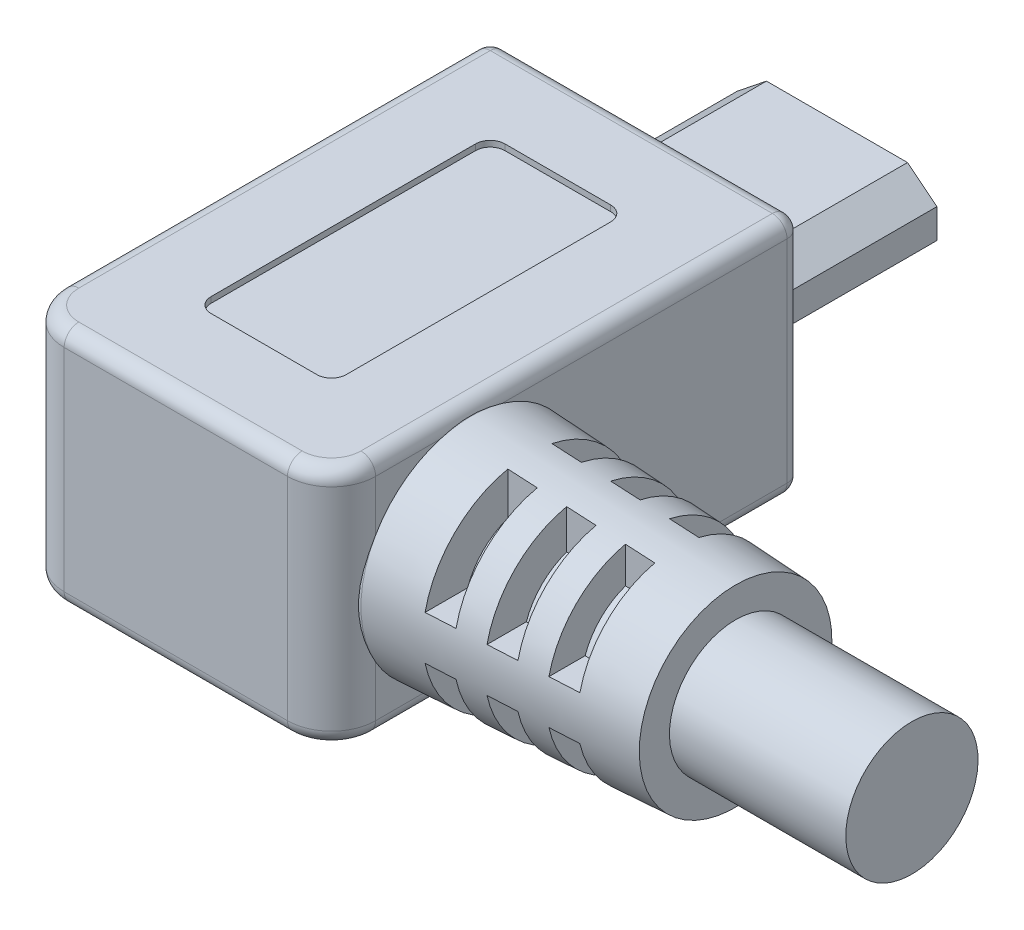
SolidWorks part; units mm, degrees
ref_plane "Front Plane" through (0, 0, 0) normal (0, 0, 1) x (1, 0, 0)
ref_plane "Top Plane" through (0, 0, 0) normal (0, 1, 0) x (1, 0, 0)
ref_plane "Right Plane" through (0, 0, 0) normal (1, 0, 0) x (0, 0, -1)
sketch "Sketch1" plane through (0, 0, 0) normal (0, 0, 1) x (1, 0, 0)
  line L0 (0, 1) -> (1, 1.8)
  line L1 (0, 0) -> (6.8, 0)
  line L2 (0, 0) -> (0, 1.8)
  line L3 (0, 1.8) -> (6.8, 1.8)
  line L4 (6.8, 0) -> (6.8, 1.8)
  line L5 (3.4, 1.8) -> (3.4, 0) construction
  line L6 (6.8, 1) -> (5.8, 1.8)
  line L8 (1.55, 0.2) -> (5.25, 0.2)
  line L9 (1.55, 0.2) -> (1.55, 0.85)
  line L10 (1.55, 0.85) -> (5.25, 0.85)
  line L11 (5.25, 0.2) -> (5.25, 0.85)
  point P15 (3.4, 0.85)
  dimension "D1" = 1.8
  dimension "D2" = 6.8
  dimension "D3" = 1
  dimension "D4" = 1
  dimension "D5" = 0.2
  dimension "D6" = 3.7
  dimension "D7" = 0.65
extrude "Boss-Extrude1" add sketch "Sketch1" along normal blind 6.5 contours L5 L3 L0 L2 L1 L8 L9 L10 | L3 L5 L10 L11 L8 L1 L4 L6
sketch "Sketch2" plane through (0, 0, 6.5) normal (0, 0, 1) x (1, 0, 0)
  line L0 (0, 0.5) -> (-1.9, 0.5) construction
  line L1 (-1.9, 5) -> (8.7, 5)
  line L2 (-1.9, 5) -> (-1.9, -3.2)
  line L3 (-1.9, -3.2) -> (8.7, -3.2)
  line L4 (8.7, 5) -> (8.7, -3.2)
  line L5 (-1.9, 2.8) -> (0.3, 5) construction
  line L6 (8.7, 2.8) -> (6.5, 5) construction
  line L8 (3.4, 5) -> (3.4, 1.8) construction
  line L9 (6.8, 0) -> (6.8, 1) construction
  line L10 (1, 1.8) -> (5.8, 1.8) construction
  line L11 (8.7, -1) -> (6.5, -3.2) construction
  line L12 (0.3, -3.2) -> (-1.9, -1) construction
  line L13 (0, 0) -> (0, 1) construction
  line L14 (6.8, 0.5) -> (8.7, 0.5) construction
  line L15 (6.8, 0) -> (6.8, 1) construction
  line L16 (3.4, 0) -> (3.4, -3.2) construction
  line L17 (0, 0) -> (6.8, 0) construction
  line M1 (1.55, 0.85) -> (5.25, 0.85)
  line M2 (5.25, 0.85) -> (5.25, 0.2)
  line M3 (5.25, 0.2) -> (1.55, 0.2)
  line M4 (1.55, 0.2) -> (1.55, 0.85)
  line M5 (6.8, 1) -> (5.8, 1.8)
  line M6 (5.8, 1.8) -> (1, 1.8)
  line M7 (1, 1.8) -> (0, 1)
  line M8 (0, 1) -> (0, 0)
  line M9 (0, 0) -> (6.8, 0)
  line M10 (6.8, 0) -> (6.8, 1)
  dimension "D1" = 10.6
  dimension "D2" = 8.2
  dimension "D3" = 2.2
  dimension "D4" = 2.2
  dimension "D5" = 2.2
  dimension "D7" = 2.2
extrude "Boss-Extrude2" add sketch "Sketch2" along normal blind 16 contours L4 L6 L1 L5 L2 L3 M5 M10 M9 M8 M7 M6 | M10 M5 M6 M7 M8 M9 M4 M1 M2 M3 | M1 M4 M3 M2
ref_plane "Plane1" through (0, 0.9, 0) normal (0, 1, 0) x (1, 0, 0)
sketch "Sketch6" plane through (0, 5, 0) normal (0, 1, 0) x (1, 0, 0)
  line L8 (5.7, -9.5) -> (1.1, -9.5)
  line L9 (1.1, -9.5) -> (1.1, -19.5)
  line L10 (1.1, -19.5) -> (5.7, -19.5)
  line L11 (5.7, -19.5) -> (5.7, -9.5)
  line L12 (5.7, -9.5) -> (1.1, -9.5)
  line L13 (1.1, -9.5) -> (1.1, -19.5)
  line L14 (1.1, -19.5) -> (5.7, -19.5)
  line L15 (5.7, -19.5) -> (5.7, -9.5)
  dimension "D1" = 3
extrude "Cut-Extrude2" cut sketch "Sketch6" against normal blind 0.2
fillet "Fillet3" radius 0.5 4 edges at (5.7, 4.9, 9.5) (1.1, 4.9, 9.5) (5.7, 4.9, 19.5) (1.1, 4.9, 19.5)
mirror "Mirror2" about plane through (0, 0.9, 0) normal (0, 1, 0) of "Fillet3", "Cut-Extrude2"
fillet "Fillet1" radius 1.5 2 edges at (-1.9, 0.9, 22.5) (8.7, 0.9, 22.5)
fillet "Fillet2" radius 0.5 14 edges at (-1.9, -3.2, 13.75) (-1.4607, -3.2, 22.0607) (3.4, -3.2, 22.5) (8.2607, -3.2, 22.0607) (-1.9, 5, 13.75) (-1.4607, 5, 22.0607) (3.4, 5, 22.5) (8.2607, 5, 22.0607) (8.7, -3.2, 13.75) (8.7, 5, 13.75) (3.4, -3.2, 6.5) (-1.9, 0.9, 6.5) (3.4, 5, 6.5) (8.7, 0.9, 6.5)
sketch "Sketch3" plane through (8.7, 0, 0) normal (1, 0, 0) x (0, 0, -1)
  line L0 (-22.5, 0.9) -> (-17.75, 0.9) construction
  line L1 (-22.5, 5) -> (-22.5, -3.2) construction
  circle A0 centre (-17.75, 0.9) radius 3.75
  dimension "D1" = 4.75
  dimension "D2" = 7.5
extrude "Boss-Extrude3" add sketch "Sketch3" along normal blind 9 draft 3 and the other way up to next (8.7 mm away)
sketch "Sketch5" plane through (0, 5, 0) normal (0, 1, 0) x (1, 0, 0)
  line L0 (17.7, -17.75) -> (8.7, -17.75) construction
  line L1 (10.7, -14.1048) -> (11.7, -14.1048)
  line L2 (10.7, -14.1048) -> (10.7, -17)
  line L3 (10.7, -17) -> (11.7, -17)
  line L4 (11.7, -14.1048) -> (11.7, -17)
  line L5 (12.7, -14.1048) -> (13.7, -14.1048)
  line L6 (12.7, -14.1048) -> (12.7, -17)
  line L7 (12.7, -17) -> (13.7, -17)
  line L8 (13.7, -14.1048) -> (13.7, -17)
  line L9 (14.7, -14.1048) -> (15.7, -14.1048)
  line L10 (14.7, -14.1048) -> (14.7, -17)
  line L11 (14.7, -17) -> (15.7, -17)
  line L12 (15.7, -14.1048) -> (15.7, -17)
  line L13 (10.7, -21.3952) -> (11.7, -21.3952)
  line L14 (10.7, -21.3952) -> (10.7, -18.5)
  line L15 (10.7, -18.5) -> (11.7, -18.5)
  line L16 (11.7, -21.3952) -> (11.7, -18.5)
  line L17 (12.7, -21.3952) -> (13.7, -21.3952)
  line L18 (12.7, -21.3952) -> (12.7, -18.5)
  line L19 (12.7, -18.5) -> (13.7, -18.5)
  line L20 (13.7, -21.3952) -> (13.7, -18.5)
  line L21 (14.7, -21.3952) -> (15.7, -21.3952)
  line L22 (14.7, -21.3952) -> (14.7, -18.5)
  line L23 (14.7, -18.5) -> (15.7, -18.5)
  line L24 (15.7, -21.3952) -> (15.7, -18.5)
  line L25 (17.7, -21.0283) -> (17.7, -14.4717) construction
  line L26 (8.7, -16.7) -> (8.7, -18.8) construction
  line L27 (11.2, -17) -> (11.2, -17.75) construction
  line L28 (11.2, -17.75) -> (11.2, -18.5) construction
  line L29 (13.2, -17) -> (13.2, -17.75) construction
  line L30 (13.2, -17.75) -> (13.2, -18.5) construction
  line L31 (15.2, -17) -> (15.2, -17.75) construction
  line L32 (15.2, -17.75) -> (15.2, -18.5) construction
  line L33 (11.7, -17) -> (12.7, -17) construction
  line L34 (13.7, -17) -> (14.7, -17) construction
  line L35 (17.7, -14.4717) -> (8.7, -14) construction
  line L36 (17.7, -17) -> (15.7, -17) construction
  line L37 (10.7, -17) -> (8.7, -17) construction
  line L38 (8.7, -16.7) -> (8.7, -14) construction
  dimension "D1" = 2
  dimension "D2" = 1
  dimension "D3" = 1.5
extrude "Cut-Extrude1" cut sketch "Sketch5" against normal offset from surface (3.35 mm away) 0.75 up to plane "Plane1"
mirror "Mirror1" about plane through (0, 0.9, 0) normal (0, 1, 0) of "Cut-Extrude1"
sketch "Sketch4" plane through (8.7, 0, 0) normal (1, 0, 0) x (0, 0, -1)
  circle A0 centre (-17.75, 0.9) radius 2.25
  dimension "D1" = 4.5
extrude "Boss-Extrude4" add sketch "Sketch4" along normal blind 15
